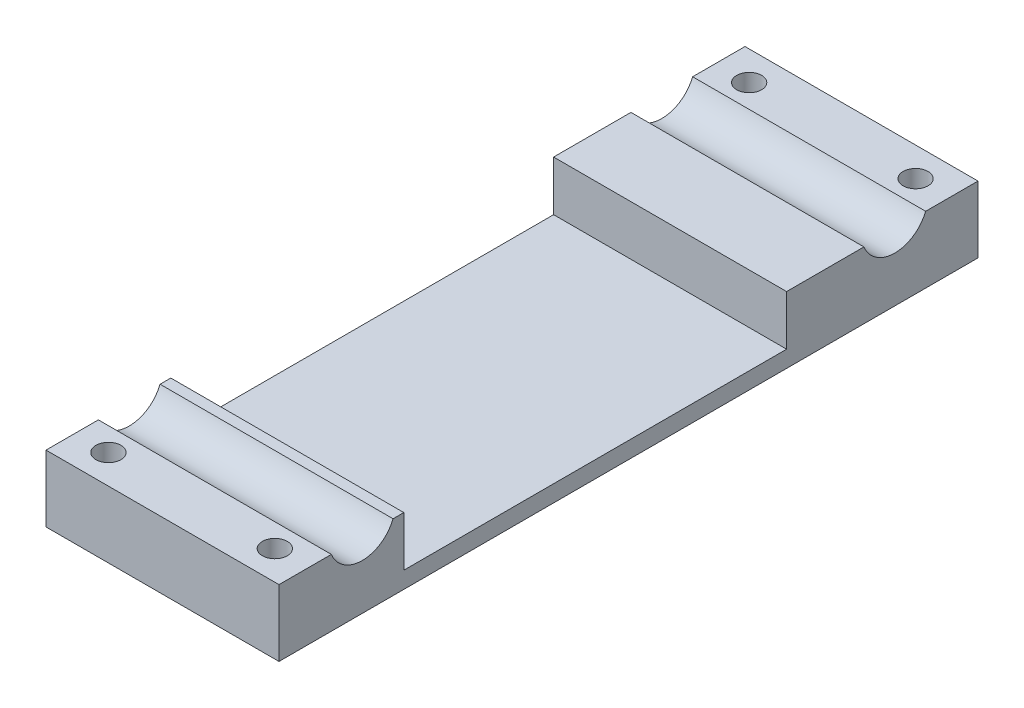
SolidWorks part; units mm, degrees
ref_plane "Front Plane" through (0, 0, 0) normal (0, 0, 1) x (1, 0, 0)
ref_plane "Top Plane" through (0, 0, 0) normal (0, 1, 0) x (1, 0, 0)
ref_plane "Right Plane" through (0, 0, 0) normal (1, 0, 0) x (0, 0, -1)
ref_plane "Plane1" through (0, 12.2427, 0) normal (0, 1, 0) x (1, 0, 0)
sketch "Sketch1" plane through (0, 12.2427, 0) normal (0, 1, 0) x (1, 0, 0)
  line L0 (-49.2685, -53.1978) -> (-21.2685, -53.1978) construction
  line L1 (-49.2685, -53.1978) -> (-49.2685, -46.9059) construction
  line L2 (-49.2685, -39.4898) -> (-49.2685, -38.1978) construction
  line L3 (-49.2685, -39.1978) -> (-49.2685, -47.1978) construction
  line L4 (-49.2685, 15.8022) -> (-49.2685, 17.0941) construction
  line L5 (-49.2685, 15.8022) -> (-49.2685, -38.1978) construction
  line L6 (-49.2685, 24.8022) -> (-49.2685, 16.8022) construction
  line L7 (-49.2685, 24.5102) -> (-49.2685, 50.8022) construction
  line L8 (-21.2685, 50.8022) -> (-49.2685, 50.8022) construction
  line L9 (-21.2685, 24.5102) -> (-21.2685, 50.8022) construction
  line L10 (-21.2685, 15.8022) -> (-21.2685, 17.0941) construction
  line L11 (-21.2685, 16.8022) -> (-21.2685, 24.8022) construction
  line L12 (-21.2685, -39.4898) -> (-21.2685, -38.1978) construction
  line L13 (-21.2685, -53.1978) -> (-21.2685, -46.9059) construction
  line L14 (-21.2685, -47.1978) -> (-21.2685, -39.1978) construction
  line L15 (-21.2685, -38.1978) -> (-21.2685, 15.8022) construction
  line L16 (-49.2685, -53.1978) -> (-21.2685, -53.1978)
  line L17 (-49.2685, -53.1978) -> (-49.2685, -46.9059)
  line L18 (-49.2685, -39.4898) -> (-49.2685, -38.1978)
  line L19 (-49.2685, -39.1978) -> (-49.2685, -47.1978)
  line L20 (-49.2685, 15.8022) -> (-49.2685, 17.0941)
  line L21 (-49.2685, 15.8022) -> (-49.2685, -38.1978)
  line L22 (-49.2685, 24.8022) -> (-49.2685, 16.8022)
  line L23 (-49.2685, 24.5102) -> (-49.2685, 50.8022)
  line L24 (-21.2685, 50.8022) -> (-49.2685, 50.8022)
  line L25 (-21.2685, 24.5102) -> (-21.2685, 50.8022)
  line L26 (-21.2685, 15.8022) -> (-21.2685, 17.0941)
  line L27 (-21.2685, 16.8022) -> (-21.2685, 24.8022)
  line L28 (-21.2685, -39.4898) -> (-21.2685, -38.1978)
  line L29 (-21.2685, -53.1978) -> (-21.2685, -46.9059)
  line L30 (-21.2685, -47.1978) -> (-21.2685, -39.1978)
  line L31 (-21.2685, -38.1978) -> (-21.2685, 15.8022)
  line L32 (-49.2685, -38.1978) -> (-21.2685, -38.1978) construction
  line L33 (-49.2685, -53.1978) -> (-21.2685, -53.1978)
  line L34 (-49.2685, -53.1978) -> (-49.2685, 30.8022)
  line L35 (-49.2685, 30.8022) -> (-21.2685, 30.8022)
  line L36 (-21.2685, -53.1978) -> (-21.2685, 30.8022)
  line L37 (-49.2685, 15.8022) -> (-21.2685, 15.8022) construction
  line L38 (-49.2685, -38.1978) -> (-21.2685, -38.1978)
  line L39 (-49.2685, 15.8022) -> (-21.2685, 15.8022)
  circle A0 centre (-25.2685, -49.6978) radius 1.5 construction
  circle A1 centre (-45.2685, -49.6978) radius 1.5 construction
  circle A2 centre (-25.2685, 27.3022) radius 1.5 construction
  circle A3 centre (-45.2685, 27.3022) radius 1.5 construction
  circle A4 centre (-25.2685, -49.6978) radius 1.5
  circle A5 centre (-45.2685, -49.6978) radius 1.5
  circle A6 centre (-25.2685, 27.3022) radius 1.5
  circle A7 centre (-45.2685, 27.3022) radius 1.5
  dimension "D1" = 84
extrude "Boss-Extrude1" add sketch "Sketch1" against normal blind 8 contours L20 L39 L26 L27 L25 L35 L23 L22 A7 A6 | L39 L21 L38 L31 | L38 L18 L19 L17 L16 L29 L30 L28 A5 A4
sketch "Sketch4" plane through (-21.2685, 0, 0) normal (1, 0, 0) x (0, 0, -1)
  line L7 (41.858, 12.2427) -> (-41.858, 12.2427) construction
  line L8 (-38.1978, 12.2427) -> (7.8022, 12.2427)
  line L9 (-38.1978, 12.2427) -> (-38.1978, 6.2427)
  line L10 (-38.1978, 6.2427) -> (7.8022, 6.2427)
  line L11 (7.8022, 12.2427) -> (7.8022, 6.2427)
  line L12 (-53.1978, 4.2427) -> (-53.1978, 12.2427) construction
  dimension "D1" = 6
  dimension "D2" = 46
  dimension "D3" = 15
extrude "Cut-Extrude1" cut sketch "Sketch4" against normal through all both and the other way through all
sketch "Sketch5" plane through (-21.2685, 0, 0) normal (1, 0, 0) x (0, 0, -1)
  line L1 (41.858, 12.2427) -> (-41.858, 12.2427) construction
  line L2 (-53.1978, 4.2427) -> (-53.1978, 12.2427) construction
  line L3 (-11.1978, -1.4549) -> (-11.1978, 29.1074) construction
  line L4 (30.8022, 4.2427) -> (30.8022, 12.2427) construction
  circle A1 centre (-43.1978, 13.7427) radius 4
  circle A2 centre (20.8022, 13.7427) radius 4
  dimension "D1" = 8
  dimension "D2" = 1.5
  dimension "D3" = 10
  dimension "D4" = 42
extrude "Cut-Extrude2" cut sketch "Sketch5" against normal through all both
